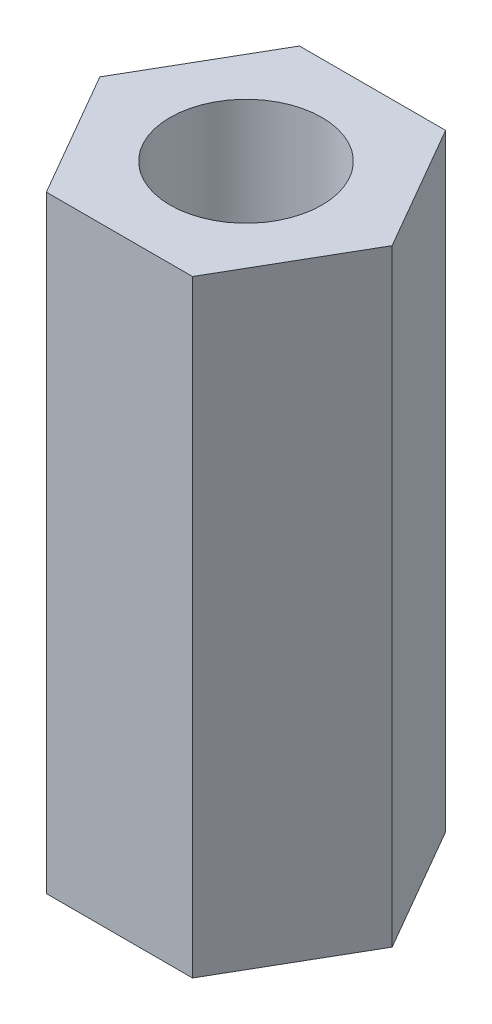
SolidWorks part; units mm, degrees
material "ABS"
ref_plane "Alzado" through (0, 0, 0) normal (0, 0, 1) x (1, 0, 0)
ref_plane "Planta" through (0, 0, 0) normal (0, 1, 0) x (1, 0, 0)
ref_plane "Vista lateral" through (0, 0, 0) normal (1, 0, 0) x (0, 0, -1)
sketch "Croquis1" plane through (0, 0, 0) normal (0, 1, 0) x (1, 0, 0)
  line L1 (1.4434, -2.5) -> (2.8868, 0)
  line L2 (2.8868, 0) -> (1.4434, 2.5)
  line L3 (1.4434, 2.5) -> (-1.4434, 2.5)
  line L4 (-1.4434, 2.5) -> (-2.8868, 0)
  line L5 (-2.8868, 0) -> (-1.4434, -2.5)
  line L6 (-1.4434, -2.5) -> (1.4434, -2.5)
  circle A0 centre (0, 0) radius 2.5 construction
  circle A1 centre (0, 0) radius 1.5
  dimension "D2" = 3
  dimension "D1" = 5
extrude "Saliente-Extruir1" add sketch "Croquis1" along normal mid plane 12
